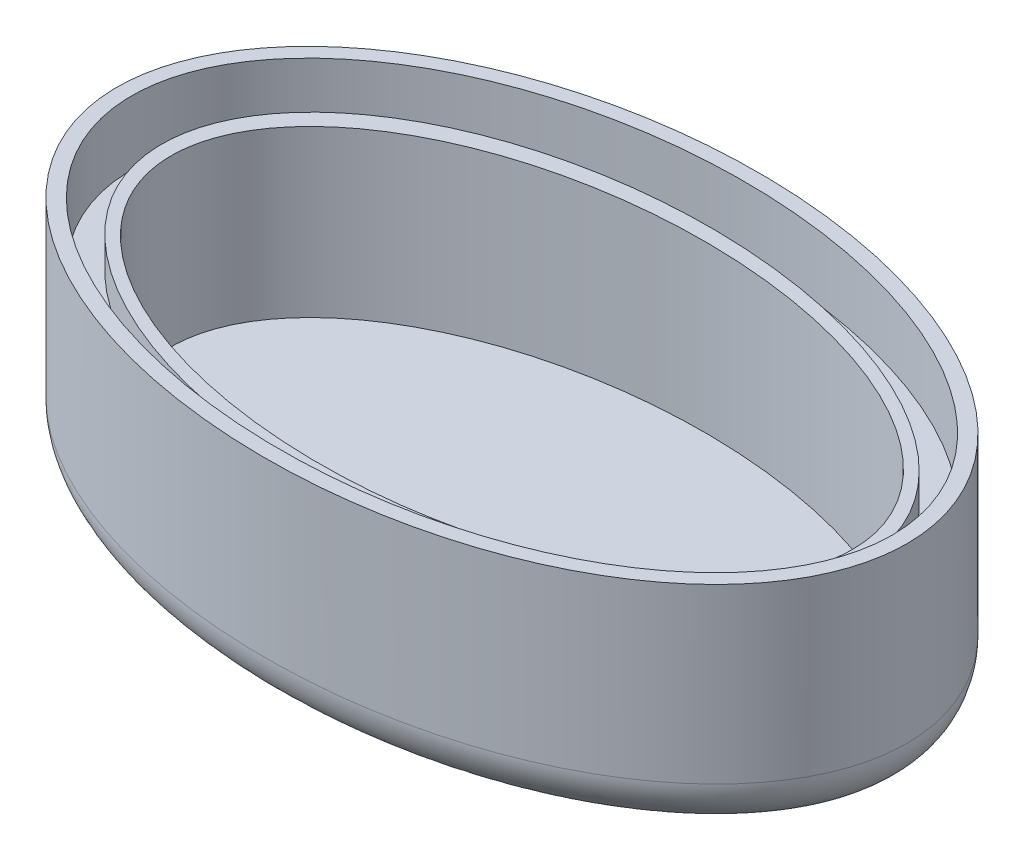
SolidWorks part; units mm, degrees
ref_plane "Front Plane" through (0, 0, 0) normal (0, 0, 1) x (1, 0, 0)
ref_plane "Top Plane" through (0, 0, 0) normal (0, 1, 0) x (1, 0, 0)
ref_plane "Right Plane" through (0, 0, 0) normal (1, 0, 0) x (0, 0, -1)
sketch "Sketch2" plane through (0, 0, 0) normal (0, 1, 0) x (1, 0, 0)
  ellipse E0 centre (0, 0) end of major axis (80, 0) minor radius 50
extrude "Boss-Extrude1" add sketch "Sketch2" along normal blind 45
fillet "Fillet2" radius 10 1 edges at (80, 0, 0)
ref_plane "top bod" through (0, 45, 0) normal (0, 1, 0) x (1, 0, 0)
sketch "Sketch3" plane through (0, 45, 0) normal (0, 1, 0) x (1, 0, 0)
  ellipse E0 centre (0, 0) end of major axis (69, 0) minor radius 39
extrude "Cut-Extrude1" cut sketch "Sketch3" against normal blind 40
sketch "Sketch4" plane through (0, 45, 0) normal (0, 1, 0) x (1, 0, 0)
  ellipse E0 centre (0, 0) end of major axis (77, 0) minor radius 47
extrude "Cut-Extrude2" cut sketch "Sketch4" against normal blind 13
ref_plane "irrigation wall" through (0, 32, 0) normal (0, 1, 0) x (1, 0, 0)
sketch "Sketch5" plane through (0, 32, 0) normal (0, 1, 0) x (1, 0, 0)
  ellipse E0 centre (0, 0) end of major axis (71.982, -1.6076) minor radius 42
  ellipse E1 centre (0, 0) end of major axis (69, 0) minor radius 39
  ellipse E2 centre (0, 0) end of major axis (69, 0) minor radius 39 construction
  ellipse E3 centre (0, 0) end of major axis (69, 0) minor radius 39 construction
extrude "Boss-Extrude2" add sketch "Sketch5" along normal blind 6.5
ref_plane "Plane3" through (0, 35, 0) normal (0, 1, 0) x (1, 0, 0)
sketch "Sketch10" plane through (0, 35, 0) normal (0, 1, 0) x (1, 0, 0)
  ellipse E0 centre (0, 0) end of major axis (69, 0) minor radius 39
  ellipse E1 centre (0, 0) end of major axis (69, 0) minor radius 39 construction
